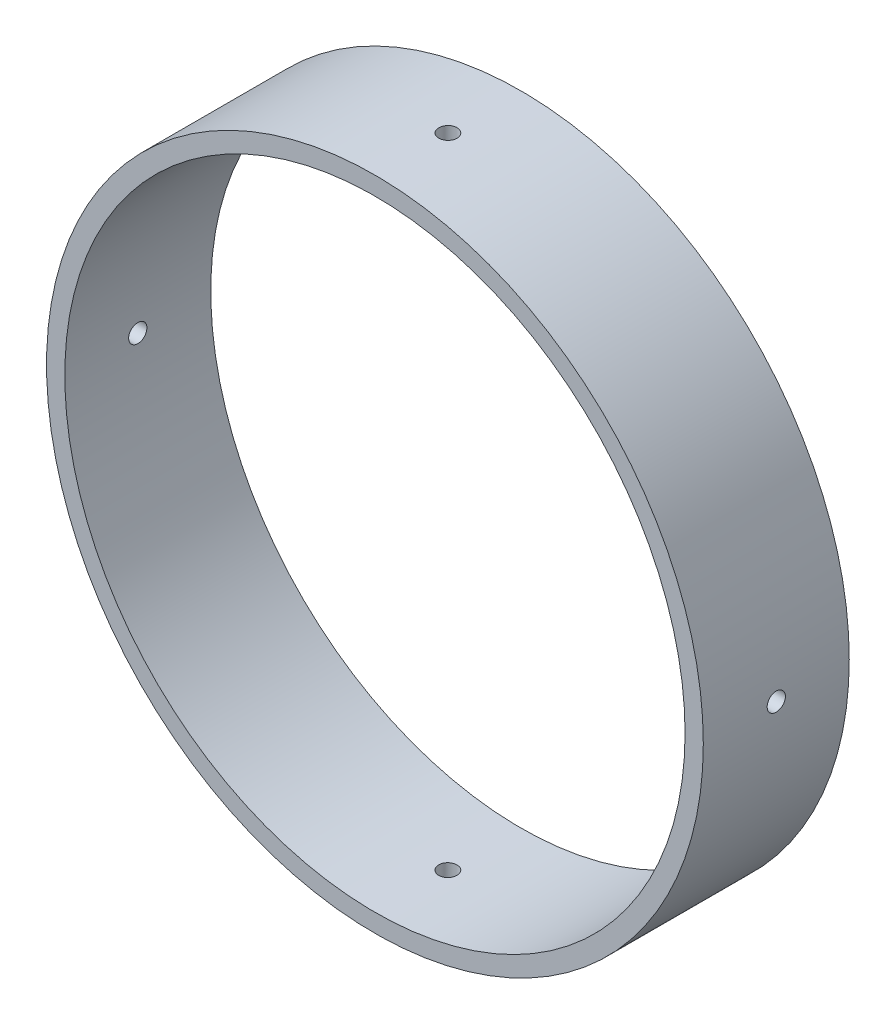
SolidWorks part; units mm, degrees
material "6061 Alloy"
ref_plane "Front Plane" through (0, 0, 0) normal (0, 0, 1) x (1, 0, 0)
ref_plane "Top Plane" through (0, 0, 0) normal (0, 1, 0) x (1, 0, 0)
ref_plane "Right Plane" through (0, 0, 0) normal (1, 0, 0) x (0, 0, -1)
sketch "Sketch1" plane through (0, 0, 0) normal (0, 0, 1) x (1, 0, 0)
  circle A0 centre (0, 0) radius 228.6
  dimension "D1" = 457.2
extrude "Boss-Extrude1" add sketch "Sketch1" along normal blind 101.6
sketch "Sketch2" plane through (0, 0, 101.6) normal (0, 0, 1) x (1, 0, 0)
  circle A0 centre (0, 0) radius 215.9
  circle A1 centre (0, 0) radius 228.6 construction
  dimension "D1" = 12.7
extrude "Cut-Extrude1" cut sketch "Sketch2" against normal through all
ref_plane "Plane1" through (0, 228.6, 0) normal (0, 1, 0) x (-1, 0, 0)
ref_plane "Plane2" through (0, -228.6, 0) normal (0, 1, 0) x (-1, 0, 0)
sketch "Sketch3" plane through (0, 228.6, 0) normal (0, 1, 0) x (-1, 0, 0)
  line L0 (-215.9, 0) -> (215.9, 0) construction
  circle A0 centre (0, 50.8) radius 6.35
  dimension "D1" = 12.7
  dimension "D2" = 50.8
extrude "Cut-Extrude2" cut sketch "Sketch3" against normal through all
ref_plane "Plane3" through (228.6, 0, 0) normal (1, 0, 0) x (0, 0, -1)
sketch "Sketch4" plane through (228.6, 0, 0) normal (1, 0, 0) x (0, 0, -1)
  line L0 (0, -228.6) -> (0, 228.6) construction
  circle A0 centre (-50.8, 0) radius 6.35
  dimension "D1" = 12.7
  dimension "D2" = 50.8
extrude "Cut-Extrude3" cut sketch "Sketch4" against normal through all
